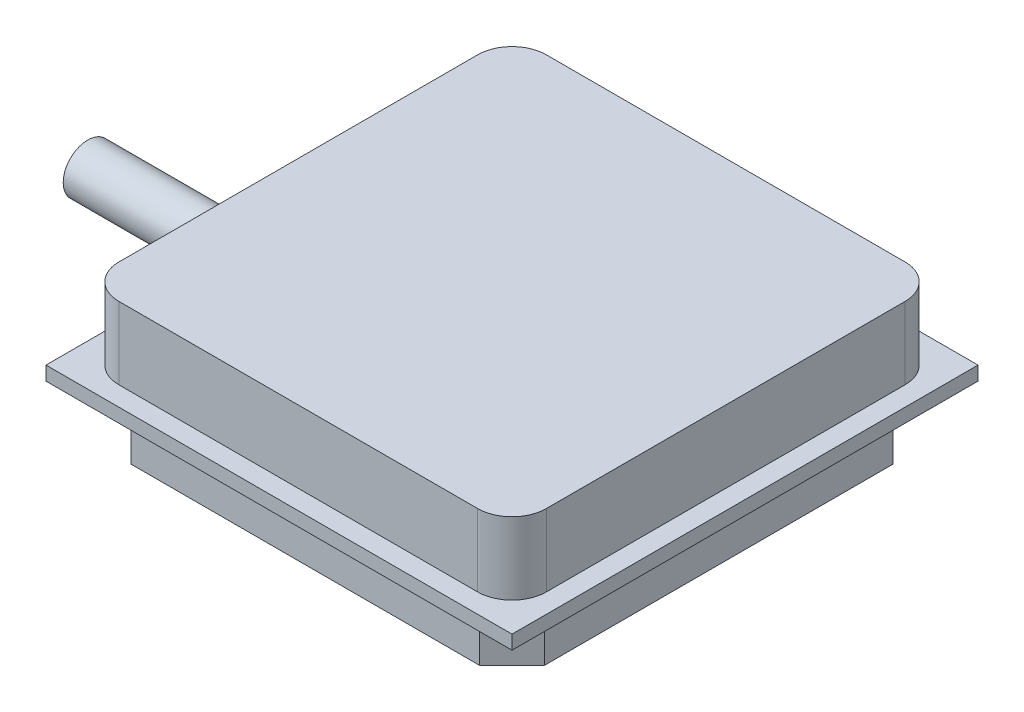
SolidWorks part; units mm, degrees
ref_plane "Front Plane" through (0, 0, 0) normal (0, 0, 1) x (1, 0, 0)
ref_plane "Top Plane" through (0, 0, 0) normal (0, 1, 0) x (1, 0, 0)
ref_plane "Right Plane" through (0, 0, 0) normal (1, 0, 0) x (0, 0, -1)
sketch "Sketch1" plane through (0, 0, 0) normal (0, 1, 0) x (1, 0, 0)
  line L1 (0, 0) -> (27.2034, 0)
  line L2 (0, 0) -> (0, 27.2034)
  line L3 (0, 27.2034) -> (27.2034, 27.2034)
  line L4 (27.2034, 0) -> (27.2034, 27.2034)
  dimension "D1" = 27.2034
  dimension "D2" = 27.2034
extrude "Boss-Extrude1" add sketch "Sketch1" along normal blind 0.8128
sketch "Sketch2" plane through (0, 0.8128, 0) normal (0, 1, 0) x (1, 0, 0)
  line L0 (26.0731, 26.0731) -> (1.1303, 1.1303) construction
  line L1 (3.1303, 26.0731) -> (24.0731, 26.0731)
  line L2 (1.1303, 24.0731) -> (1.1303, 3.1303)
  line L3 (3.1303, 1.1303) -> (24.0731, 1.1303)
  line L4 (26.0731, 24.0731) -> (26.0731, 3.1303)
  line L5 (0, 27.2034) -> (27.2034, 0) construction
  arc A0 (1.1303, 3.1303) -> (3.1303, 1.1303) centre (3.1303, 3.1303) ccw
  arc A1 (24.0731, 1.1303) -> (26.0731, 3.1303) centre (24.0731, 3.1303) ccw
  arc A2 (24.0731, 26.0731) -> (26.0731, 24.0731) centre (24.0731, 24.0731) cw
  arc A3 (3.1303, 26.0731) -> (1.1303, 24.0731) centre (3.1303, 24.0731) ccw
  point P4 (13.6017, 13.6017)
  point P6 (13.6017, 13.6017)
  point P21 (1.1303, 26.0731)
  dimension "D3" = 2
  dimension "D1" = 24.9428
  dimension "D2" = 24.9428
extrude "Boss-Extrude2" add sketch "Sketch2" along normal blind 4.2164
sketch "Sketch3" plane through (0, 0, 0) normal (0, -1, 0) x (1, 0, 0)
  line L0 (1.5367, -1.5367) -> (25.6667, -25.6667) construction
  line L1 (1.5367, -1.5367) -> (25.6667, -1.5367)
  line L2 (1.5367, -1.5367) -> (1.5367, -25.6667)
  line L3 (1.5367, -25.6667) -> (25.6667, -25.6667)
  line L4 (25.6667, -1.5367) -> (25.6667, -25.6667)
  line L5 (27.2034, 0) -> (0, -27.2034) construction
  line L6 (-8.6334, -13.6017) -> (13.6017, 8.6334)
  line L7 (-8.6334, -13.6017) -> (13.6017, -35.8368)
  line L8 (13.6017, 8.6334) -> (35.8368, -13.6017)
  line L9 (13.6017, -35.8368) -> (35.8368, -13.6017)
  line L10 (-8.6334, -13.6017) -> (35.8368, -13.6017) construction
  line L11 (35.8368, -13.6017) -> (31.2289, -18.2096) construction
  point P8 (13.6017, -13.6017)
  point P13 (13.6017, -13.6017)
  dimension "D1" = 45
  dimension "D2" = 24.13
  dimension "D3" = 24.13
  dimension "D4" = 31.4452
  dimension "D5" = 31.4452
extrude "Boss-Extrude3" add sketch "Sketch3" along normal blind 3.2512 contours L3 L9 L4 L8 L1 L6 L2 L7
sketch "Sketch4" plane through (1.5367, 0, 0) normal (-1, 0, 0) x (0, 0, 1)
  line L0 (-23.7718, -3.2512) -> (-3.4316, 0) construction
  circle A0 centre (-13.6017, -1.6256) radius 1.4351
  dimension "D1" = 2.8702
extrude "Boss-Extrude4" add sketch "Sketch4" along normal blind 12.7
